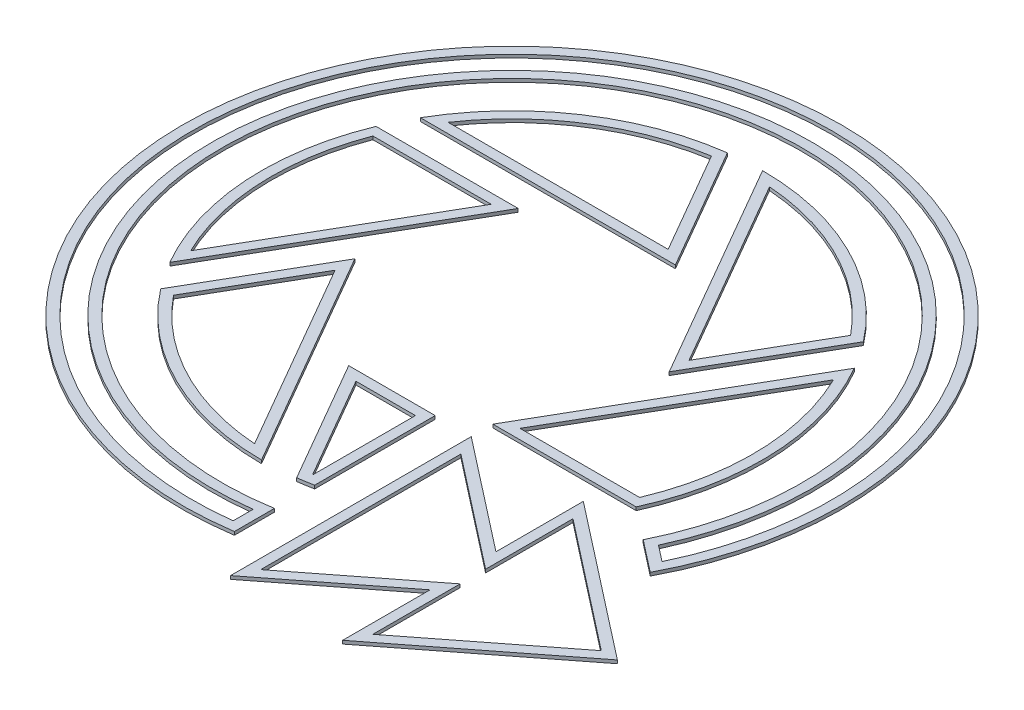
SolidWorks part; units mm, degrees
ref_plane "前视基准面" through (0, 0, 0) normal (0, 0, 1) x (1, 0, 0)
ref_plane "上视基准面" through (0, 0, 0) normal (0, 1, 0) x (1, 0, 0)
ref_plane "右视基准面" through (0, 0, 0) normal (1, 0, 0) x (0, 0, -1)
other "Configuration Table"
sketch "草图1" plane through (0, 0, 0) normal (0, 1, 0) x (1, 0, 0)
  line L0 (-2097.4547, -11.9316) -> (-770.8759, -11.9316) construction
  line L1 (-109.6966, 190) -> (-329.0897, 190)
  line L2 (128.4499, -157.5182) -> (219.3931, 0)
  line L3 (193.4123, 45) -> (109.6966, 190)
  line L4 (57.735, 190) -> (-109.6966, 190)
  line L5 (-135.6773, 145) -> (-219.3931, 0)
  line L6 (-193.4123, -45) -> (-109.6966, -190)
  line L7 (-57.735, -190) -> (73.4499, -190)
  line L8 (-135.6773, 145) -> (-351.2478, 145)
  line L9 (-219.3931, 0) -> (-329.0897, -190)
  line L10 (-193.4123, -45) -> (-301.1976, -231.6895)
  line L11 (-109.6966, -190) -> (0, -380)
  line L12 (-57.735, -190) -> (50.0502, -376.6895)
  line L13 (73.4499, -190) -> (73.4499, -372.8339)
  line L14 (-50.0502, 376.6895) -> (57.735, 190)
  line L15 (109.6966, 190) -> (0, 380)
  line L16 (219.3931, 0) -> (329.0897, 190)
  line L17 (301.1976, 231.6895) -> (193.4123, 45)
  line L18 (128.4499, -157.5182) -> (345.815, -157.5182)
  line L19 (128.4499, -190.3339) -> (128.4499, -555.3339)
  line L20 (128.4499, -555.3339) -> (298.4499, -422.8339)
  line L21 (298.4499, -422.8339) -> (298.4499, -555.3339)
  line L22 (298.4499, -555.3339) -> (532.6009, -372.8339)
  line L26 (128.4499, -372.8339) -> (532.6009, -372.8339) construction
  line L30 (298.4499, -190.3339) -> (532.6009, -372.8339)
  line L31 (298.4499, -322.8339) -> (298.4499, -190.3339)
  line L32 (128.4499, -190.3339) -> (298.4499, -322.8339)
  line L33 (73.4499, -433.8261) -> (73.4499, -494.5757)
  line L34 (394.2838, -195.2953) -> (442.4701, -232.8523)
  circle A3 centre (0, 0) radius 190 construction
  arc A4 (394.2838, -195.2953) -> (73.4499, -433.8261) centre (0, 0) ccw
  arc A5 (442.4701, -232.8523) -> (73.4499, -494.5757) centre (0, 0) ccw
  arc A6 (50.0502, -376.6895) -> (73.4499, -372.8339) centre (0, 0) ccw
  arc A7 (-301.1976, -231.6895) -> (0, -380) centre (0, 0) ccw
  arc A8 (-351.2478, 145) -> (-329.0897, -190) centre (0, 0) ccw
  arc A9 (-50.0502, 376.6895) -> (-329.0897, 190) centre (0, 0) ccw
  arc A10 (301.1976, 231.6895) -> (0, 380) centre (0, 0) ccw
  arc A11 (345.815, -157.5182) -> (329.0897, 190) centre (0, 0) ccw
  dimension "D2" = 500
  dimension "D12" = 380
  dimension "D5" = 45
  dimension "D7" = 219.3931
  dimension "D6" = 45
  dimension "D8" = 45
  dimension "D9" = 45
  dimension "D10" = 45
  dimension "D11" = 51.9615
  dimension "D14" = 55
  dimension "D13" = 365
  dimension "D15" = 170
  dimension "D16" = 100
  dimension "D17" = 55
  dimension "D3" = 60
  dimension "D4" = 60
extrude "凸台-拉伸1" add sketch "草图1" along normal blind 5
sketch "草图2" plane through (0, 5, 0) normal (0, 1, 0) x (1, 0, 0)
  line L0 (-161.6581, 130) -> (-341.0645, 130)
  line L1 (-328.5319, -159.0339) -> (-232.3835, 7.5)
  line L2 (73.4499, -494.5757) -> (73.4499, -433.8261)
  line L3 (-135.6773, 145) -> (-351.2478, 145)
  line L4 (-219.3931, 0) -> (-135.6773, 145)
  line L5 (-329.0897, -190) -> (-219.3931, 0)
  line L6 (-135.6773, 145) -> (-351.2478, 145) construction
  line L7 (-219.3931, 0) -> (-135.6773, 145) construction
  line L8 (-329.0897, -190) -> (-219.3931, 0) construction
  line L9 (73.4499, -190) -> (-57.735, -190)
  line L10 (73.4499, -372.8339) -> (73.4499, -190)
  line L11 (-57.735, -190) -> (50.0502, -376.6895)
  line L12 (73.4499, -190) -> (-57.735, -190) construction
  line L13 (73.4499, -372.8339) -> (73.4499, -190) construction
  line L14 (-57.735, -190) -> (50.0502, -376.6895) construction
  line L15 (-193.4123, -45) -> (-301.1976, -231.6895)
  line L16 (0, -380) -> (-109.6966, -190)
  line L17 (-109.6966, -190) -> (-193.4123, -45)
  line L18 (-193.4123, -45) -> (-301.1976, -231.6895) construction
  line L19 (0, -380) -> (-109.6966, -190) construction
  line L20 (-109.6966, -190) -> (-193.4123, -45) construction
  line L21 (57.735, 190) -> (-50.0502, 376.6895)
  line L22 (-329.0897, 190) -> (-109.6966, 190)
  line L23 (-109.6966, 190) -> (57.735, 190)
  line L24 (57.735, 190) -> (-50.0502, 376.6895) construction
  line L25 (-329.0897, 190) -> (-109.6966, 190) construction
  line L26 (-109.6966, 190) -> (57.735, 190) construction
  line L27 (109.6966, 190) -> (193.4123, 45)
  line L28 (0, 380) -> (109.6966, 190)
  line L29 (193.4123, 45) -> (301.1976, 231.6895)
  line L30 (109.6966, 190) -> (193.4123, 45) construction
  line L31 (0, 380) -> (109.6966, 190) construction
  line L32 (193.4123, 45) -> (301.1976, 231.6895) construction
  line L33 (329.0897, 190) -> (219.3931, 0)
  line L34 (219.3931, 0) -> (128.4499, -157.5182)
  line L35 (128.4499, -157.5182) -> (345.815, -157.5182)
  line L36 (329.0897, 190) -> (219.3931, 0) construction
  line L37 (-232.3835, 7.5) -> (-161.6581, 130)
  line L38 (58.4499, -205) -> (-31.7543, -205)
  line L39 (-31.7543, -205) -> (57.949, -360.3705)
  line L40 (58.4499, -360.2896) -> (58.4499, -205)
  line L41 (-193.4123, -75) -> (-283.1156, -230.3705)
  line L42 (-26.5385, -364.0339) -> (-122.6869, -197.5)
  line L43 (-122.6869, -197.5) -> (-193.4123, -75)
  line L51 (219.3931, 0) -> (128.4499, -157.5182) construction
  line L52 (128.4499, -157.5182) -> (345.815, -157.5182) construction
  line L53 (394.2838, -195.2953) -> (442.4701, -232.8523)
  line L54 (73.4499, -494.5757) -> (73.4499, -433.8261) construction
  line L55 (394.2838, -195.2953) -> (442.4701, -232.8523) construction
  line L56 (31.7543, 205) -> (-57.949, 360.3705)
  line L57 (-301.9934, 205) -> (-109.6966, 205)
  line L58 (-109.6966, 205) -> (31.7543, 205)
  line L59 (122.6869, 197.5) -> (193.4123, 75)
  line L60 (193.4123, 75) -> (283.1156, 230.3705)
  line L61 (26.5385, 364.0339) -> (122.6869, 197.5)
  line L62 (328.5319, 159.0339) -> (232.3835, -7.5)
  line L63 (232.3835, -7.5) -> (154.4307, -142.5182)
  line L64 (154.4307, -142.5182) -> (336.0261, -142.5182)
  line L65 (58.4499, -481.4651) -> (58.4499, -451.2301)
  line L66 (413.0236, -190.8834) -> (437.2798, -209.7889)
  line L81 (313.4499, -392.1247) -> (313.4499, -524.6247)
  line L82 (313.4499, -524.6247) -> (508.2005, -372.8339)
  line L83 (508.2005, -372.8339) -> (313.4499, -221.043)
  line L84 (313.4499, -221.043) -> (313.4499, -353.543)
  line L85 (313.4499, -353.543) -> (143.4499, -221.043)
  line L86 (143.4499, -221.043) -> (143.4499, -524.6247)
  line L87 (143.4499, -524.6247) -> (313.4499, -392.1247)
  line L88 (313.4499, -392.1247) -> (313.4499, -524.6247)
  line L89 (313.4499, -524.6247) -> (508.2005, -372.8339)
  line L90 (508.2005, -372.8339) -> (313.4499, -221.043)
  line L91 (313.4499, -221.043) -> (313.4499, -353.543)
  line L92 (313.4499, -353.543) -> (143.4499, -221.043)
  line L93 (143.4499, -221.043) -> (143.4499, -524.6247)
  line L94 (143.4499, -524.6247) -> (313.4499, -392.1247)
  arc A0 (-341.0645, 130) -> (-328.5319, -159.0339) centre (0, 0) ccw
  arc A1 (-351.2478, 145) -> (-329.0897, -190) centre (0, 0) ccw
  arc A2 (-351.2478, 145) -> (-329.0897, -190) centre (0, 0) ccw construction
  arc A3 (50.0502, -376.6895) -> (73.4499, -372.8339) centre (0, 0) ccw
  arc A4 (50.0502, -376.6895) -> (73.4499, -372.8339) centre (0, 0) ccw construction
  arc A5 (-301.1976, -231.6895) -> (0, -380) centre (0, 0) ccw
  arc A6 (-301.1976, -231.6895) -> (0, -380) centre (0, 0) ccw construction
  arc A7 (-50.0502, 376.6895) -> (-329.0897, 190) centre (0, 0) ccw
  arc A8 (-50.0502, 376.6895) -> (-329.0897, 190) centre (0, 0) ccw construction
  arc A9 (301.1976, 231.6895) -> (0, 380) centre (0, 0) ccw
  arc A10 (301.1976, 231.6895) -> (0, 380) centre (0, 0) ccw construction
  arc A11 (345.815, -157.5182) -> (329.0897, 190) centre (0, 0) ccw
  arc A12 (345.815, -157.5182) -> (329.0897, 190) centre (0, 0) ccw construction
  arc A13 (57.949, -360.3705) -> (58.4499, -360.2896) centre (0, 0) ccw
  arc A14 (394.2838, -195.2953) -> (73.4499, -433.8261) centre (0, 0) ccw
  arc A15 (442.4701, -232.8523) -> (73.4499, -494.5757) centre (0, 0) ccw
  arc A16 (394.2838, -195.2953) -> (73.4499, -433.8261) centre (0, 0) ccw construction
  arc A17 (442.4701, -232.8523) -> (73.4499, -494.5757) centre (0, 0) ccw construction
  arc A18 (-283.1156, -230.3705) -> (-26.5385, -364.0339) centre (0, 0) ccw
  arc A19 (-57.949, 360.3705) -> (-301.9934, 205) centre (0, 0) ccw
  arc A20 (283.1156, 230.3705) -> (26.5385, 364.0339) centre (0, 0) ccw
  arc A21 (336.0261, -142.5182) -> (328.5319, 159.0339) centre (0, 0) ccw
  arc A22 (413.0236, -190.8834) -> (58.4499, -451.2301) centre (0, 0) ccw
  arc A23 (437.2798, -209.7889) -> (58.4499, -481.4651) centre (0, 0) ccw
  dimension "D9" = 15
  dimension "D1" = 0
  dimension "D2" = 0
  dimension "D3" = 0
  dimension "D4" = 0
  dimension "D5" = 0
  dimension "D6" = 15
  dimension "D7" = 0
  dimension "D8" = 0
extrude "切除-拉伸1" cut sketch "草图2" against normal blind 5
equation "\"D6@草图1\"=\"D5@草图1\""
equation "\"D8@草图1\"=\"D5@草图1\""
equation "\"D10@草图1\"=\"D5@草图1\""
equation "\"D14@草图1\"=\"D17@草图1\""
equation "\"D4@草图1\"=\"D3@草图1\""
